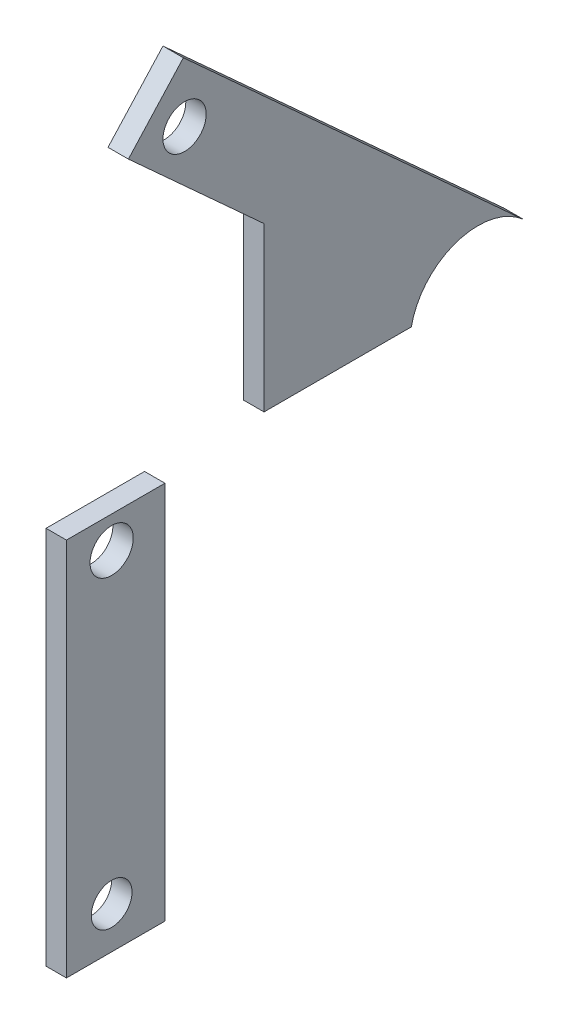
SolidWorks part; units mm, degrees
ref_plane "Alzado" through (0, 0, 0) normal (0, 0, 1) x (1, 0, 0)
ref_plane "Planta" through (0, 0, 0) normal (0, 1, 0) x (1, 0, 0)
ref_plane "Vista lateral" through (0, 0, 0) normal (1, 0, 0) x (0, 0, -1)
sketch "Croquis1" plane through (0, 0, 0) normal (1, 0, 0) x (0, 0, -1)
  line L0 (73.5577, 13.8733) -> (-9.9503, 90.0009)
  line L1 (-9.9503, 90.0009) -> (-23.4242, 75.2207)
  line L2 (-23.4242, 75.2207) -> (9.8312, 44.9044)
  line L3 (9.8312, 44.9044) -> (9.8312, 4.9044)
  line L4 (9.8312, 4.9044) -> (45.9503, 4.9044)
  line L5 (-72.7622, -82.0394) -> (30.7863, -79.323) construction
  line L6 (-14.4673, 1.9261) -> (-14.4673, -91.0615)
  line L7 (-38.6115, 1.9261) -> (-14.4673, 1.9261)
  line L8 (-14.4673, -91.0615) -> (-38.6115, -91.0615)
  line L9 (-38.6115, -91.0615) -> (-38.6115, 1.9261)
  arc A0 (73.5577, 13.8733) -> (45.9503, 4.9044) centre (62.3067, 1.5315) ccw
  circle A1 centre (-9.6511, 75.2403) radius 5.3
  circle A2 centre (-27.5313, -5.827) radius 5.3
  circle A3 centre (-27.5313, -80.8528) radius 5
extrude "Saliente-Extruir1" add sketch "Croquis1" along normal blind 5
